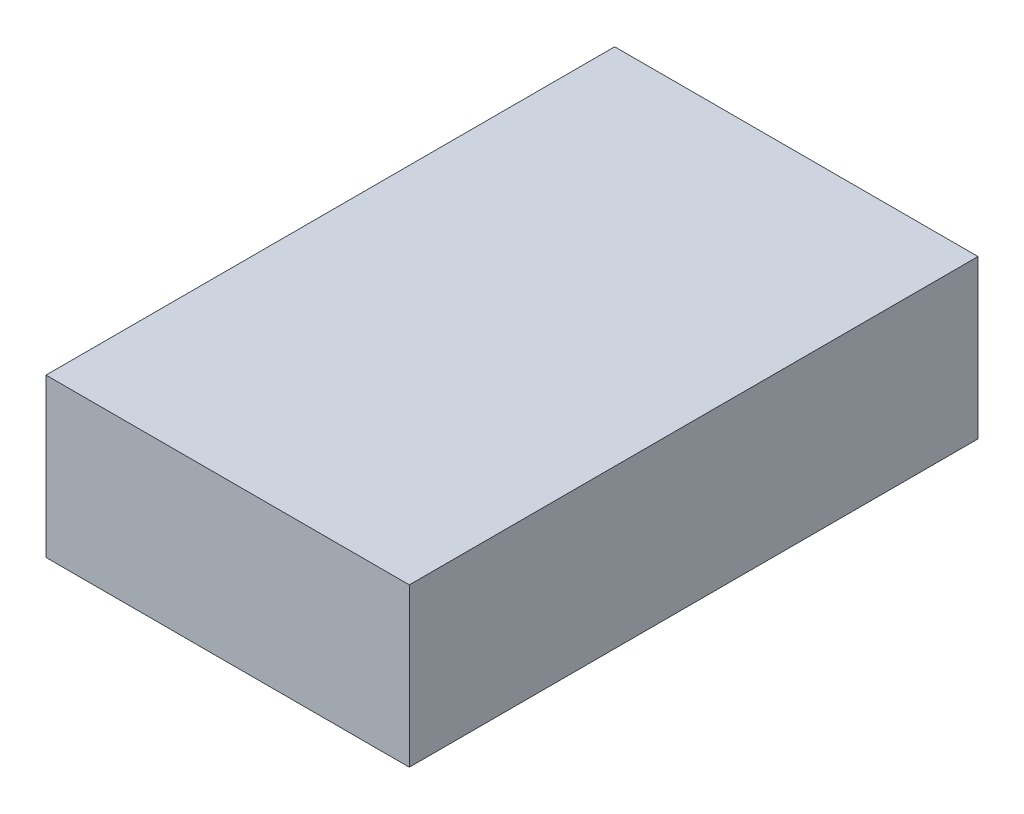
SolidWorks part; units mm, degrees
ref_plane "Front Plane" through (0, 0, 0) normal (0, 0, 1) x (1, 0, 0)
ref_plane "Top Plane" through (0, 0, 0) normal (0, 1, 0) x (1, 0, 0)
ref_plane "Right Plane" through (0, 0, 0) normal (1, 0, 0) x (0, 0, -1)
sketch "Sketch1" plane through (0, 0, 0) normal (0, 1, 0) x (1, 0, 0)
  line L1 (-11.2997, 1.8833) -> (11.7003, 1.8833)
  line L2 (-11.2997, 1.8833) -> (-11.2997, -34.1167)
  line L3 (-11.2997, -34.1167) -> (11.7003, -34.1167)
  line L4 (11.7003, 1.8833) -> (11.7003, -34.1167)
  dimension "D1" = 23
  dimension "D2" = 36
extrude "Boss-Extrude1" add sketch "Sketch1" along normal blind 10
